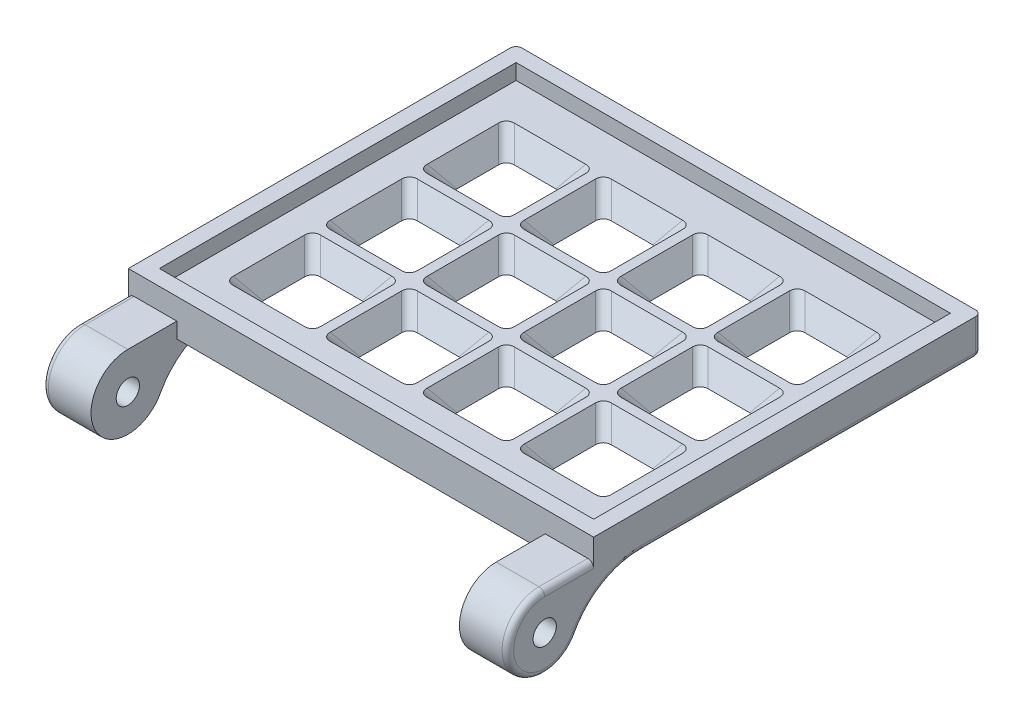
SolidWorks part; units mm, degrees
ref_plane "Front Plane" through (0, 0, 0) normal (0, 0, 1) x (1, 0, 0)
ref_plane "Top Plane" through (0, 0, 0) normal (0, 1, 0) x (1, 0, 0)
ref_plane "Right Plane" through (0, 0, 0) normal (1, 0, 0) x (0, 0, -1)
sketch "Sketch1" plane through (0, 0, 0) normal (0, 1, 0) x (1, 0, 0)
  line L1 (30.48, -25.4) -> (-30.48, -25.4)
  line L2 (30.48, -25.4) -> (30.48, 25.4)
  line L3 (30.48, 25.4) -> (-30.48, 25.4)
  line L4 (-30.48, -25.4) -> (-30.48, 25.4)
  line L5 (30.48, -25.4) -> (-30.48, 25.4) construction
  line L6 (30.48, 25.4) -> (-30.48, -25.4) construction
  point P0 (0, 0)
  dimension "D1" = 50.8
  dimension "D2" = 60.96
extrude "Boss-Extrude1" add sketch "Sketch1" along normal blind 3.048
sketch "Sketch2" plane through (0, 3.048, 0) normal (0, 1, 0) x (1, 0, 0)
  line L0 (-19.05, 18.415) -> (-19.05, 25.4) construction
  line L1 (-13.335, 6.985) -> (-24.765, 6.985)
  line L2 (-13.335, 6.985) -> (-13.335, 18.415)
  line L3 (-13.335, 18.415) -> (-24.765, 18.415)
  line L4 (-24.765, 6.985) -> (-24.765, 18.415)
  line L5 (30.48, 25.4) -> (-30.48, 25.4) construction
  line L6 (-24.765, 12.7) -> (-30.48, 12.7) construction
  line L7 (-30.48, 25.4) -> (-30.48, -25.4) construction
  dimension "D1" = 11.43
  dimension "D2" = 5.715
  dimension "D3" = 6.985
extrude "Cut-Extrude1" cut sketch "Sketch2" against normal blind 3.048 draft 35
fillet "Fillet1" radius 1.27 4 edges at (-23.6979, 1.524, -8.0521) (-14.4021, 1.524, -8.0521) (-14.4021, 1.524, -17.3479) (-23.6979, 1.524, -17.3479)
pattern_linear "LPattern1" count 4 spacing 12.7 along (1, 0, 0) count 3 spacing 12.7 along (0, 0, 1) of "Fillet1", "Cut-Extrude1"
ref_plane "Plane1" through (30.48, 3.048, 25.4) normal (1, 0, 0) x (0, 0, -1)
sketch "Sketch9" plane through (0, 3.048, 0) normal (0, 1, 0) x (1, 0, 0)
  line L0 (30.48, -42.164) -> (30.48, -8.636) construction
  line L1 (-30.48, 25.4) -> (30.48, 25.4)
  line L2 (-30.48, 25.4) -> (-30.48, -25.4)
  line L3 (-30.48, -25.4) -> (30.48, -25.4)
  line L4 (30.48, 25.4) -> (30.48, -25.4)
  line L5 (-30.48, -25.4) -> (30.48, -25.4) construction
  line L6 (-28.448, 23.368) -> (-28.448, -23.368)
  line L7 (-28.448, -23.368) -> (28.448, -23.368)
  line L8 (28.448, 23.368) -> (28.448, -23.368)
  line L9 (-28.448, 23.368) -> (28.448, 23.368)
  dimension "D1" = 2.032
extrude "Boss-Extrude2" add sketch "Sketch9" along normal blind 2.032
sketch "Sketch11" plane through (0, 0, 0) normal (0, -1, 0) x (1, 0, 0)
  line L0 (30.48, 8.636) -> (30.48, 42.164) construction
  line L1 (-30.48, 25.4) -> (30.48, 25.4)
  line L2 (-30.48, 25.4) -> (-30.48, -30.48)
  line L3 (-30.48, -30.48) -> (30.48, -30.48)
  line L4 (30.48, 25.4) -> (30.48, -30.48)
extrude "Cut-Extrude3" cut sketch "Sketch11" against normal blind 0.254
ref_plane "Plane2" through (0, 2.286, 0) normal (0, 1, 0) x (1, 0, 0)
sketch "Sketch14" plane through (30.48, 0, 0) normal (1, 0, 0) x (0, 0, -1)
  line L0 (-25.4, 2.286) -> (-26.9875, 2.286) construction
  line L1 (27.94, 2.286) -> (-27.94, 2.286) construction
  line L2 (-25.4, 5.08) -> (-25.4, 0.254) construction
  line L3 (-31.8135, 2.286) -> (-25.4, 2.286) construction
  line L5 (-25.4, 2.286) -> (-31.8135, 2.286)
  line L6 (-26.9875, -2.54) -> (-26.9875, 2.286) construction
  line L7 (-25.4, 0.254) -> (-26.9875, 0.254)
  line L8 (-26.9875, 0.254) -> (-26.9875, -2.54)
  line L10 (-25.4, 0.254) -> (-23.368, 0.254)
  line L12 (25.4, 0.254) -> (-25.4, 0.254) construction
  line L13 (-23.368, 0.254) -> (-23.368, 2.286)
  line L14 (-23.368, 2.286) -> (-25.4, 2.286)
  arc A0 (-31.8135, 2.286) -> (-26.9875, -2.54) centre (-31.8135, -2.54) ccw
  circle A1 centre (-31.8135, -2.54) radius 1.524
  dimension "D1" = 9.652
  dimension "D2" = 3.048
  dimension "D3" = 1.5875
  dimension "D4" = 2.032
extrude "Boss-Extrude3" add sketch "Sketch14" against normal blind 6.35
ref_plane "Plane3" through (0, 0, 0) normal (-1, 0, 0) x (0, 0, 1)
sketch "Sketch15" plane through (30.48, 3.048, 25.4) normal (1, 0, 0) x (0, 0, -1)
  line L0 (6.2823, -2.794) -> (-1.5875, -2.794)
  line L1 (-1.5875, -2.794) -> (-2.1546, -7.8578)
  line L2 (50.8, -2.794) -> (-1.5875, -2.794) construction
  arc A0 (-2.1546, -7.8578) -> (6.2823, -2.794) centre (6.2823, -12.3543) cw
  arc A1 (-6.4135, -0.762) -> (-1.5875, -5.588) centre (-6.4135, -5.588) ccw construction
  dimension "D1" = 9.5603
extrude "Boss-Extrude4" add sketch "Sketch15" against normal up to surface (6.35 mm away) up to face at (24.13, -2.54, 30.2895)
mirror "Mirror3" about plane through (0, 0, 0) normal (-1, 0, 0) of "Boss-Extrude4", "Boss-Extrude3"
fillet "Fillet9" radius 0.762 11 edges at (-30.48, 2.286, 28.6068) (-30.48, -5.0236, 35.9514) (-30.48, -1.1091, 24.0377) (-30.48, 0.254, -3.1411) (30.48, 2.286, 28.6068) (30.48, -5.0236, 35.9514) (30.48, -1.1091, 24.0377) (30.48, 0.254, -3.1411) (-30.48, 2.667, -25.4) (30.48, 2.667, -25.4) (0, 0.254, -25.4)
sketch "Sketch16" plane through (0, 0.254, 0) normal (0, -1, 0) x (1, 0, 0)
  line L5 (-15.2564, -16.4856) -> (-22.7666, -16.4856)
  line L6 (-15.2564, -16.4856) -> (-15.2564, -8.9282)
  line L7 (-15.2564, -8.9282) -> (-22.7666, -8.9282)
  line L8 (-22.7666, -16.4856) -> (-22.7666, -8.9282)
  dimension "D1" = 7.5101
